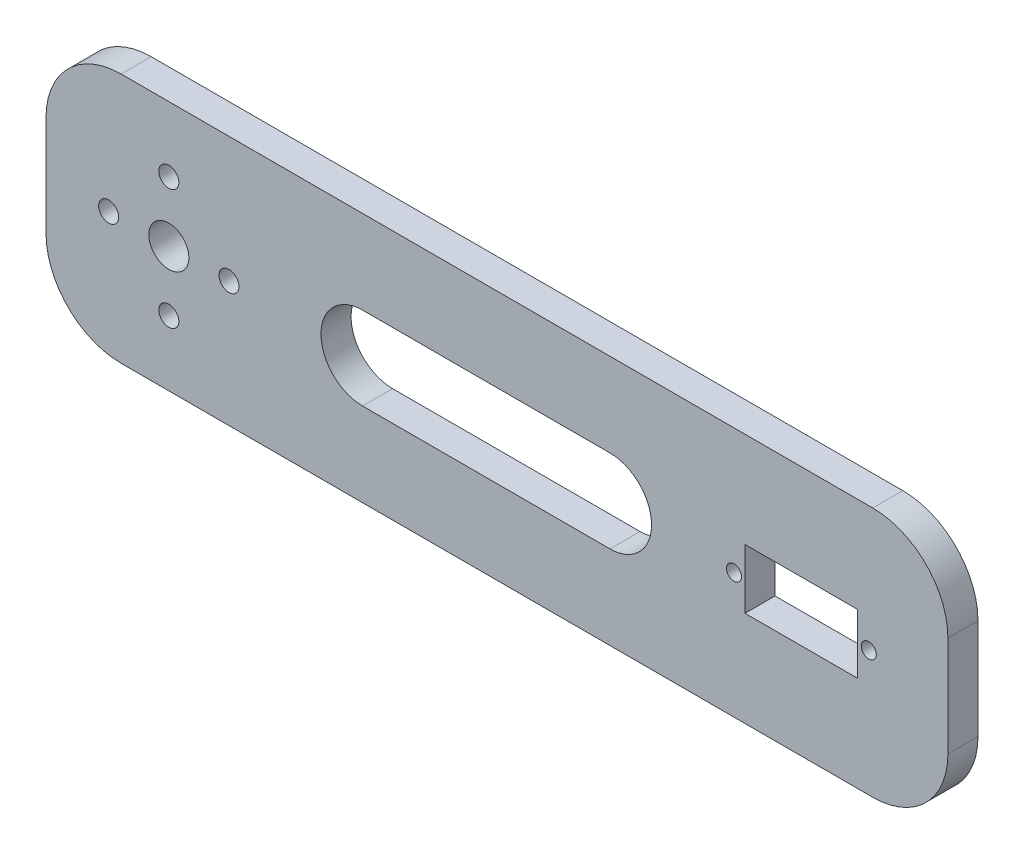
SolidWorks part; units mm, degrees
ref_plane "Front Plane" through (0, 0, 0) normal (0, 0, 1) x (1, 0, 0)
ref_plane "Top Plane" through (0, 0, 0) normal (0, 1, 0) x (1, 0, 0)
ref_plane "Right Plane" through (0, 0, 0) normal (1, 0, 0) x (0, 0, -1)
sketch "Sketch1" plane through (0, 0, 0) normal (0, 0, 1) x (1, 0, 0)
  line L1 (-72.4404, 25) -> (107.5596, 25)
  line L2 (-72.4404, 25) -> (-72.4404, -25)
  line L3 (-72.4404, -25) -> (107.5596, -25)
  line L4 (107.5596, 25) -> (107.5596, -25)
  line L5 (-72.4404, 25) -> (107.5596, -25) construction
  line L6 (-72.4404, -25) -> (107.5596, 25) construction
  point P0 (0, 0)
  dimension "D1" = 180
  dimension "D2" = 50
extrude "Boss-Extrude1" add sketch "Sketch1" along normal mid plane 6
fillet "Fillet1" radius 15 4 edges at (-72.4404, -25, 0) (-72.4404, 25, 0) (107.5596, -25, 0) (107.5596, 25, 0)
sketch "Sketch3" plane through (0, 0, 3) normal (0, 0, 1) x (1, 0, 0)
  line L0 (-133.9593, 0) -> (-95.7585, 0) construction
  line L1 (-47.9262, -15.4334) -> (-47.9262, 22.0078) construction
  circle A0 centre (-47.9262, 0) radius 4
  circle A1 centre (-47.9262, 12) radius 2
  circle A2 centre (-47.9262, -12) radius 2
  circle A3 centre (-59.9262, 0) radius 2
  circle A4 centre (-35.9262, 0) radius 2
  dimension "D1" = 8
  dimension "D2" = 4
  dimension "D4" = 4
  dimension "D3" = 12
  dimension "D5" = 12
extrude "Cut-Extrude1" cut sketch "Sketch3" against normal blind 8
sketch "Sketch4" plane through (0, 0, 3) normal (0, 0, 1) x (1, 0, 0)
  line L0 (33.8417, 0) -> (95.1065, 0) construction
  line L1 (67.0596, 5.95) -> (89.5596, 5.95)
  line L2 (67.0596, 5.95) -> (67.0596, -5.95)
  line L3 (67.0596, -5.95) -> (89.5596, -5.95)
  line L4 (89.5596, 5.95) -> (89.5596, -5.95)
  line L5 (67.0596, 5.95) -> (89.5596, -5.95) construction
  line L6 (67.0596, -5.95) -> (89.5596, 5.95) construction
  line L7 (107.5596, -10) -> (107.5596, 10) construction
  line L8 (-9.2699, 0) -> (40.116, 0) construction
  line L11 (-9.2699, 8.2879) -> (40.116, 8.2879)
  line L12 (-9.2699, -8.2879) -> (40.116, -8.2879)
  circle A0 centre (64.8596, 0) radius 1.5
  circle A1 centre (91.7596, 0) radius 1.5
  arc A4 (-9.2699, 8.2879) -> (-9.2699, -8.2879) centre (-9.2699, 0) ccw
  arc A5 (40.116, -8.2879) -> (40.116, 8.2879) centre (40.116, 0) ccw
  point P0 (78.3096, 0)
  point P16 (15.4231, 0)
  dimension "D5" = 3
  dimension "D6" = 3
  dimension "D1" = 22.5
  dimension "D2" = 11.9
  dimension "D3" = 0
  dimension "D4" = 18
  dimension "D7" = 2.2
  dimension "D8" = 2.2
extrude "Cut-Extrude2" cut sketch "Sketch4" against normal blind 10
